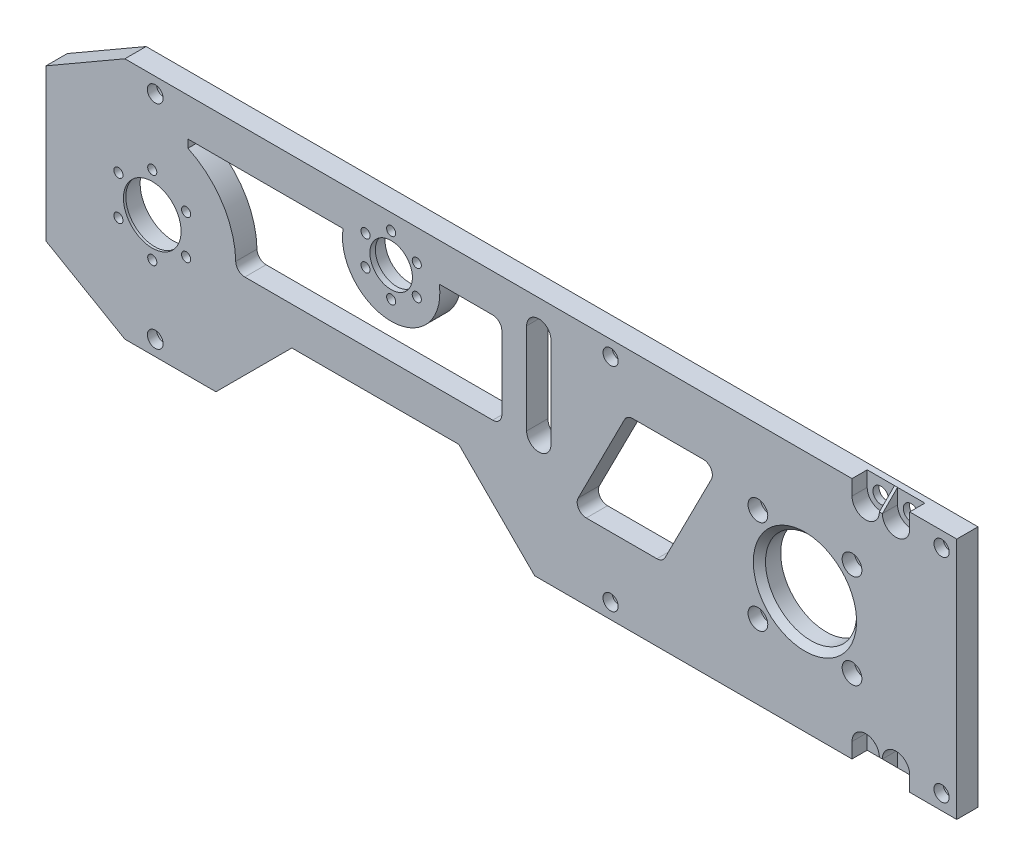
SolidWorks part; units mm, degrees
ref_plane "Front Plane" through (0, 0, 0) normal (0, 0, 1) x (1, 0, 0)
ref_plane "Top Plane" through (0, 0, 0) normal (0, 1, 0) x (1, 0, 0)
ref_plane "Right Plane" through (0, 0, 0) normal (1, 0, 0) x (0, 0, -1)
sketch "Sketch1" plane through (0, 0, 0) normal (0, 0, 1) x (1, 0, 0)
  line L1 (0, 0) -> (300, 0)
  line L2 (0, 0) -> (0, 80)
  line L3 (0, 80) -> (300, 80)
  line L4 (300, 0) -> (300, 80)
  dimension "D1" = 300
  dimension "D2" = 80
extrude "Boss-Extrude1" add sketch "Sketch1" along normal blind 7
chamfer "Chamfer1" distance 15 angle 60 1 edges at (0, 0, 3.5)
chamfer "Chamfer3" distance 15 angle 60 1 edges at (0, 80, 3.5)
sketch "Sketch2" plane through (0, 0, 7) normal (0, 0, 1) x (1, 0, 0)
  line L0 (0, 65) -> (0, 15) construction
  circle A0 centre (35, 40) radius 11
  dimension "D1" = 35
  dimension "D2" = 22
extrude "Cut-Extrude1" cut sketch "Sketch2" against normal blind 10
sketch "Sketch3" plane through (0, 0, 7) normal (0, 0, 1) x (1, 0, 0)
  circle A0 centre (35, 40) radius 9.5
  circle A1 centre (35, 40) radius 11
  dimension "D1" = 19
extrude "Boss-Extrude3" add sketch "Sketch3" against normal blind 0.8
sketch "Sketch4" plane through (0, 0, 7) normal (0, 0, 1) x (1, 0, 0)
  line L0 (162.3249, 70) -> (162.3249, 40) construction
  line L1 (163.3249, 70) -> (163.3249, 40)
  line L2 (161.3249, 70) -> (161.3249, 40)
  line L3 (300, 80) -> (25.9808, 80) construction
  arc A0 (163.3249, 70) -> (161.3249, 70) centre (162.3249, 70) ccw
  arc A1 (161.3249, 40) -> (163.3249, 40) centre (162.3249, 40) ccw
  point P2 (162.3249, 55)
  dimension "D1" = 1
  dimension "D2" = 10
  dimension "D3" = 30
extrude "Cut-Extrude2" cut sketch "Sketch4" against normal through all
sketch "Sketch5" plane through (0, 0, 7) normal (0, 0, 1) x (1, 0, 0)
  line L0 (300, 0) -> (300, 80) construction
  circle A0 centre (250, 40) radius 15
  dimension "D1" = 30
  dimension "D2" = 50
extrude "Cut-Extrude3" cut sketch "Sketch5" against normal through all
sketch "Sketch6" plane through (0, 0, 0) normal (0, 0, -1) x (-1, 0, 0)
  line L0 (-162.3249, 70) -> (-162.3249, 40) construction
  line L1 (-158.3249, 70) -> (-158.3249, 40)
  line L2 (-166.3249, 70) -> (-166.3249, 40)
  arc A0 (-158.3249, 70) -> (-166.3249, 70) centre (-162.3249, 70) ccw
  arc A1 (-166.3249, 40) -> (-158.3249, 40) centre (-162.3249, 40) ccw
  point P4 (-162.3249, 55)
  dimension "D1" = 4
extrude "Cut-Extrude4" cut sketch "Sketch6" against normal blind 8
sketch "Sketch7" plane through (0, 0, 7) normal (0, 0, 1) x (1, 0, 0)
  circle A0 centre (113.6916, 65) radius 8
  dimension "D1" = 16
extrude "Cut-Extrude6" cut sketch "Sketch7" against normal through all
sketch "Sketch8" plane through (0, 0, 7) normal (0, 0, 1) x (1, 0, 0)
  circle A0 centre (113.6916, 65) radius 8
  circle A1 centre (113.6916, 65) radius 7
  dimension "D1" = 14
extrude "Boss-Extrude4" add sketch "Sketch8" against normal blind 1.8
sketch "Sketch9" plane through (0, 0, 0) normal (0, 0, -1) x (-1, 0, 0)
  circle A0 centre (-113.6916, 65) radius 9.75
  circle A1 centre (-113.6916, 74.75) radius 1.5
  circle A2 centre (-105.2479, 69.875) radius 1.5
  circle A3 centre (-105.2479, 60.125) radius 1.5
  circle A4 centre (-113.6916, 55.25) radius 1.5
  circle A5 centre (-122.1354, 60.125) radius 1.5
  circle A6 centre (-122.1354, 69.875) radius 1.5
  point P17 (-113.6916, 65)
  dimension "D1" = 3
  dimension "D2" = 19.5
  dimension "D3" = 6
extrude "Cut-Extrude7" cut sketch "Sketch9" against normal through all contours A1 | A2 | A3 | A4 | A5 | A6
sketch "Sketch10" plane through (0, 0, 0) normal (0, 0, -1) x (-1, 0, 0)
  circle A0 centre (-113.6916, 65) radius 12
  dimension "D1" = 24
extrude "Cut-Extrude8" cut sketch "Sketch10" against normal blind 1
sketch "Sketch11" plane through (0, 0, 0) normal (0, 0, -1) x (-1, 0, 0)
  circle A0 centre (-35, 40) radius 12.875
  circle A1 centre (-35, 52.875) radius 1.5
  circle A2 centre (-23.8499, 46.4375) radius 1.5
  circle A3 centre (-23.8499, 33.5625) radius 1.5
  circle A4 centre (-35, 27.125) radius 1.5
  circle A5 centre (-46.1501, 33.5625) radius 1.5
  circle A6 centre (-46.1501, 46.4375) radius 1.5
  point P17 (-35, 40)
  dimension "D1" = 25.75
  dimension "D2" = 3
  dimension "D3" = 6
extrude "Cut-Extrude9" cut sketch "Sketch11" against normal through all contours A6 | A1 | A2 | A3 | A4 | A5
sketch "Sketch12" plane through (0, 0, 0) normal (0, 0, -1) x (-1, 0, 0)
  line L0 (-300, 80) -> (-25.9808, 80) construction
  line L1 (0, 40) -> (-11.6864, 40) construction
  line L2 (0, 65) -> (0, 15) construction
  line L3 (-300, 0) -> (-300, 80) construction
  circle A0 centre (-35.9808, 75) radius 2.6
  circle A1 centre (-185.9808, 75) radius 2.5
  circle A2 centre (-295, 75) radius 2.5
  circle A3 centre (-35.9808, 5) radius 2.6
  circle A4 centre (-185.9808, 5) radius 2.5
  circle A5 centre (-295, 5) radius 2.5
  dimension "D1" = 5.2
  dimension "D2" = 10
  dimension "D3" = 5
  dimension "D4" = 150
  dimension "D5" = 5
  dimension "D6" = 5
  dimension "D7" = 5
extrude "Cut-Extrude10" cut sketch "Sketch12" against normal through all
sketch "Sketch13" plane through (0, 0, 0) normal (0, 0, -1) x (-1, 0, 0)
  circle A0 centre (-295, 75) radius 4
  circle A1 centre (-185.9808, 75) radius 4
  circle A2 centre (-35.9808, 75) radius 4
  circle A3 centre (-35.9808, 5) radius 4
  circle A4 centre (-185.9808, 5) radius 4
  circle A5 centre (-295, 5) radius 4
  dimension "D1" = 8
  dimension "D2" = 8
  dimension "D3" = 8
  dimension "D4" = 8
  dimension "D5" = 8
  dimension "D6" = 8
extrude "Cut-Extrude11" cut sketch "Sketch13" against normal blind 4
sketch "Sketch14" plane through (0, 0, 7) normal (0, 0, 1) x (1, 0, 0)
  line L1 (234.5, 55.5) -> (265.5, 55.5)
  line L2 (234.5, 55.5) -> (234.5, 24.5)
  line L3 (234.5, 24.5) -> (265.5, 24.5)
  line L4 (265.5, 55.5) -> (265.5, 24.5)
  circle A0 centre (250, 40) radius 15 construction
  circle A1 centre (234.5, 55.5) radius 1.75
  circle A2 centre (265.5, 55.5) radius 1.75
  circle A3 centre (234.5, 24.5) radius 1.75
  circle A4 centre (265.5, 24.5) radius 1.75
  dimension "D5" = 3.5
  dimension "D6" = 3.5
  dimension "D7" = 3.5
  dimension "D8" = 3.5
  dimension "D1" = 31
  dimension "D2" = 31
  dimension "D3" = 15.5
  dimension "D4" = 15.5
extrude "Cut-Extrude12" cut sketch "Sketch14" against normal through all contours A1 | A3 | A4 | A2
sketch "Sketch15" plane through (0, 0, 7) normal (0, 0, 1) x (1, 0, 0)
  line L0 (55.9808, 0) -> (80.9808, 25)
  line L1 (25.9808, 0) -> (300, 0) construction
  line L2 (80.9808, 25) -> (135.9808, 25)
  line L3 (135.9808, 25) -> (160.9808, 0)
  line L4 (55.9808, 0) -> (160.9808, 0)
  dimension "D1" = 55
  dimension "D2" = 30
  dimension "D3" = 25
  dimension "D4" = 45
extrude "Cut-Extrude13" cut sketch "Sketch15" against normal through all
sketch "Sketch16" plane through (0, 0, 7) normal (0, 0, 1) x (1, 0, 0)
  line L0 (173.0745, 25) -> (191.3983, 61)
  line L1 (191.3983, 61) -> (221.3983, 61)
  line L2 (221.3983, 61) -> (203.0745, 25)
  line L3 (203.0745, 25) -> (173.0745, 25)
  line L4 (135.9808, 25) -> (80.9808, 25) construction
  dimension "D1" = 30
  dimension "D2" = 36
extrude "Cut-Extrude14" cut sketch "Sketch16" against normal through all
sketch "Sketch17" plane through (0, 0, 7) normal (0, 0, 1) x (1, 0, 0)
  line L0 (129.5374, 67.5) -> (150.1486, 67.5)
  line L1 (46.7546, 67.5) -> (97.8459, 67.5)
  line L3 (62.3861, 37.5) -> (150.1486, 37.5)
  line L4 (150.1486, 67.5) -> (150.1486, 37.5)
  line L5 (46.7546, 67.5) -> (46.7546, 64.8612)
  arc A0 (62.3861, 37.5) -> (46.7546, 64.8612) centre (35, 40) ccw
  arc A1 (97.8459, 67.5) -> (129.5374, 67.5) centre (113.6916, 65) ccw
  dimension "D1" = 55
  dimension "D2" = 30
extrude "Cut-Extrude15" cut sketch "Sketch17" against normal through all
sketch "Sketch18" plane through (0, 0, 7) normal (0, 0, 1) x (1, 0, 0)
  circle A0 centre (234.5, 55.5) radius 3.25
  arc A1 (236.9621, 57.6214) -> (232.3786, 53.0379) centre (250, 40) ccw
  arc A2 (232.3786, 26.9621) -> (232.3786, 53.0379) centre (250, 40) ccw
  circle A3 centre (265.5, 55.5) radius 3.25
  arc A4 (229.0375, 33.5911) -> (232.3786, 53.0379) centre (250, 40) ccw
  circle A5 centre (265.5, 24.5) radius 3.25
  circle A6 centre (250, 40) radius 21.9203
  circle A7 centre (234.5, 24.5) radius 3.25
  arc A8 (232.3786, 26.9621) -> (263.0379, 57.6214) centre (250, 40) ccw
  point P18 (250, 40)
  dimension "D2" = 6.5
  dimension "D1" = 4
extrude "Cut-Extrude16" cut sketch "Sketch18" against normal blind 4 contours A0 | A3 | A5 | A7
chamfer "Chamfer4" distance 2 angle 45 1 edges at (265, 40, 7)
fillet "Fillet1" radius 3 4 edges at (221.3983, 61, 3.5) (191.3983, 61, 3.5) (203.0745, 25, 3.5) (173.0745, 25, 3.5)
fillet "Fillet2" radius 3 3 edges at (150.1486, 67.5, 3.5) (150.1486, 37.5, 3.5) (62.3861, 37.5, 3.5)
sketch "Sketch19" plane through (0, 0, 0) normal (0, 0, -1) x (-1, 0, 0)
  line L0 (-300, 40) -> (-285.6663, 40) construction
  line L1 (-300, 0) -> (-300, 80) construction
  circle A0 centre (-280, 75) radius 2.6
  circle A1 centre (-270, 75) radius 2.6
  circle A2 centre (-295, 75) radius 2.5 construction
  circle A3 centre (-270, 5) radius 2.6
  circle A4 centre (-280, 5) radius 2.6
  dimension "D1" = 5.2
  dimension "D2" = 5.2
  dimension "D3" = 15
  dimension "D4" = 10
extrude "Cut-Extrude17" cut sketch "Sketch19" against normal through all
sketch "Sketch20" plane through (0, 0, 7) normal (0, 0, 1) x (1, 0, 0)
  line L0 (300, 40) -> (282.8306, 40) construction
  line L1 (300, 0) -> (300, 80) construction
  circle A0 centre (270, 75) radius 4.5
  circle A1 centre (280, 75) radius 4.5
  circle A2 centre (280, 5) radius 4.5
  circle A3 centre (270, 5) radius 4.5
  dimension "D1" = 9
  dimension "D2" = 9
extrude "Cut-Extrude18" cut sketch "Sketch20" against normal blind 5
sketch "Sketch21" plane through (0, 0, 7) normal (0, 0, 1) x (1, 0, 0)
  line L0 (300, 80) -> (25.9808, 80) construction
  line L1 (265.5, 75) -> (274.5, 75)
  line L2 (265.5, 75) -> (265.5, 80)
  line L3 (265.5, 80) -> (274.5, 80)
  line L4 (274.5, 75) -> (274.5, 80)
  line L5 (160.9808, 0) -> (300, 0) construction
  line L6 (275.5, 75) -> (284.5, 75)
  line L7 (275.5, 75) -> (275.5, 80)
  line L8 (275.5, 80) -> (284.5, 80)
  line L9 (284.5, 75) -> (284.5, 80)
  line L10 (265.5, 5) -> (274.5, 5)
  line L11 (265.5, 5) -> (265.5, 0)
  line L12 (265.5, 0) -> (274.5, 0)
  line L13 (274.5, 5) -> (274.5, 0)
  line L15 (275.5, 5) -> (284.5, 5)
  line L16 (275.5, 5) -> (275.5, 0)
  line L17 (275.5, 0) -> (284.5, 0)
  line L18 (284.5, 5) -> (284.5, 0)
  circle A0 centre (270, 75) radius 4.5 construction
  circle A1 centre (270, 75) radius 4.5 construction
  circle A2 centre (280, 75) radius 4.5 construction
  circle A3 centre (270, 5) radius 4.5 construction
  circle A4 centre (270, 5) radius 4.5 construction
  circle A5 centre (280, 5) radius 4.5 construction
  circle A6 centre (280, 5) radius 4.5 construction
extrude "Cut-Extrude19" cut sketch "Sketch21" against normal blind 5
chamfer "Chamfer5" distance 5 angle 45 2 edges at (275, 0, 7) (275, 80, 7)
